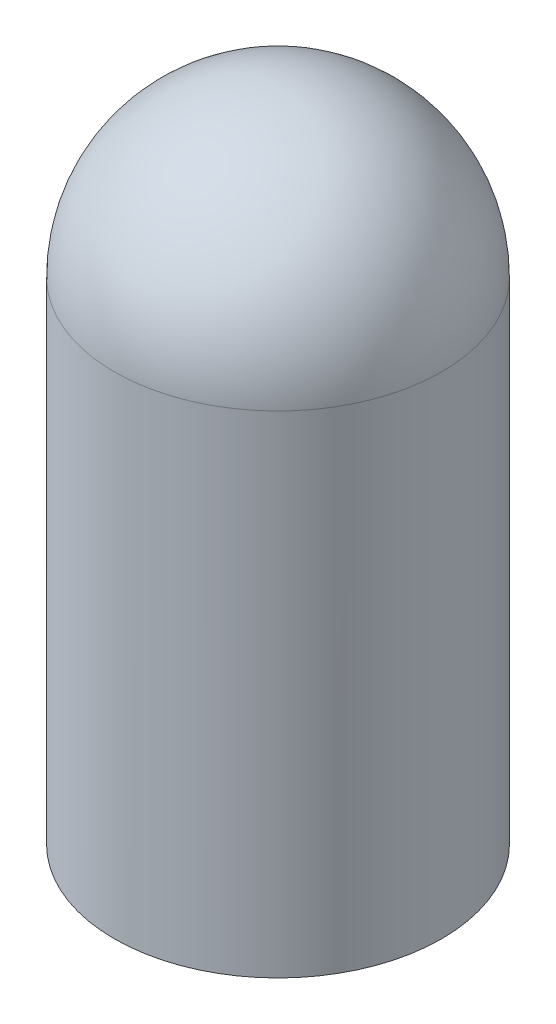
SolidWorks part; units mm, degrees
ref_plane "Front Plane" through (0, 0, 0) normal (0, 0, 1) x (1, 0, 0)
ref_plane "Top Plane" through (0, 0, 0) normal (0, 1, 0) x (1, 0, 0)
ref_plane "Right Plane" through (0, 0, 0) normal (1, 0, 0) x (0, 0, -1)
sketch "Sketch1" plane through (0, 0, 0) normal (0, 1, 0) x (1, 0, 0)
  circle A0 centre (0, 0) radius 2.413
  dimension "D1" = 4.826
extrude "Extrude1" add sketch "Sketch1" along normal blind 9.652
fillet "Fillet1" radius 2.413 1 edges at (0, 9.652, 2.413)
